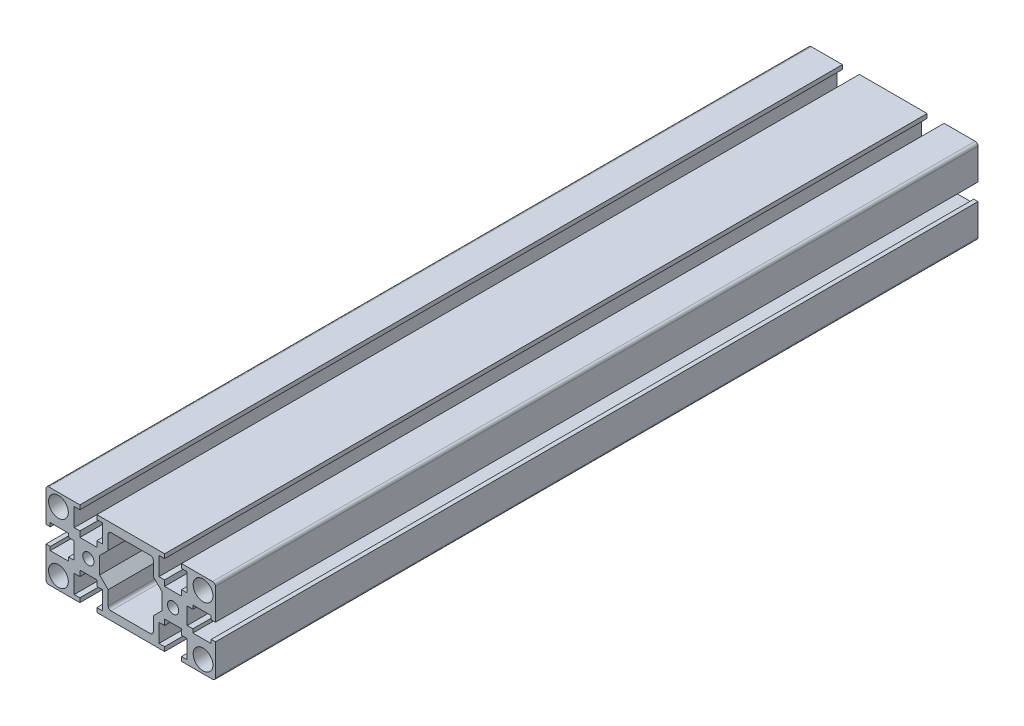
SolidWorks part; units mm, degrees
ref_plane "Front Plane" through (0, 0, 0) normal (0, 0, 1) x (1, 0, 0)
ref_plane "Top Plane" through (0, 0, 0) normal (0, 1, 0) x (1, 0, 0)
ref_plane "Right Plane" through (0, 0, 0) normal (1, 0, 0) x (0, 0, -1)
sketch "Sketch1" plane through (0, 0, 0) normal (0, 0, 1) x (1, 0, 0)
  line L0 (-49.2543, 0) -> (49.2543, 0) construction
  line L1 (-15, -15) -> (15, -15) construction
  line L2 (-15, -15) -> (-15, 14) construction
  line L3 (-14, 15) -> (15, 15) construction
  line L4 (15, -15) -> (15, 15) construction
  line L5 (-15, -15) -> (15, 15) construction
  line L6 (-15, 15) -> (15, -15) construction
  line L7 (-5, -3) -> (-5, 3)
  line L8 (-5, 3) -> (-7, 3)
  line L9 (-7, 3) -> (-7, 4.2984)
  line L10 (-7, 4.2984) -> (-13.5, 4.2984)
  line L11 (-13.5, 4.2984) -> (-13.5, 3)
  line L12 (-13.5, 3) -> (-15, 3)
  line L13 (-15, 3) -> (-15, 14)
  line L14 (-14, 15) -> (-3, 15)
  line L15 (-3, 15) -> (-3, 13.5)
  line L16 (-3, 13.5) -> (-5, 13.5)
  line L17 (-5, 13.5) -> (-5, 7)
  line L18 (-5, 7) -> (-3, 7)
  line L19 (-3, 7) -> (-3, 5)
  line L20 (-3, 5) -> (3, 5)
  line L21 (3, 15) -> (3, 13.5)
  line L22 (3, 13.5) -> (5, 13.5)
  line L23 (5, 13.5) -> (5, 7)
  line L24 (5, 7) -> (3, 7)
  line L25 (3, 7) -> (3, 5)
  line L26 (0, -31.6943) -> (0, 31.6943) construction
  line L27 (3, 15) -> (27, 15)
  line L28 (4, -3) -> (4, 3)
  line L29 (4, 3) -> (7, 6)
  line L30 (7, 6) -> (7, 11)
  line L31 (8, 12) -> (22, 12)
  line L32 (5, -7) -> (3, -7)
  line L33 (4, -3) -> (7, -6)
  line L34 (7, -6) -> (7, -11)
  line L35 (8, -12) -> (22, -12)
  line L36 (3, -15) -> (27, -15)
  line L37 (3, -15) -> (3, -13.5)
  line L38 (3, -13.5) -> (5, -13.5)
  line L39 (5, -13.5) -> (5, -7)
  line L40 (3, -7) -> (3, -5)
  line L41 (-3, -5) -> (3, -5)
  line L42 (-3, -7) -> (-3, -5)
  line L43 (-5, -7) -> (-3, -7)
  line L44 (-5, -13.5) -> (-5, -7)
  line L45 (-3, -13.5) -> (-5, -13.5)
  line L46 (-3, -15) -> (-3, -13.5)
  line L47 (-14, -15) -> (-3, -15)
  line L48 (-13.5, -3) -> (-15, -3)
  line L49 (-15, -3) -> (-15, -14)
  line L50 (-13.5, -4.2984) -> (-13.5, -3)
  line L51 (-7, -4.2984) -> (-13.5, -4.2984)
  line L52 (-7, -3) -> (-7, -4.2984)
  line L53 (-5, -3) -> (-7, -3)
  line L54 (26, 3) -> (23, 6)
  line L55 (23, 6) -> (23, 11)
  line L56 (27, 15) -> (27, 13.5)
  line L57 (27, 13.5) -> (25, 13.5)
  line L58 (25, 13.5) -> (25, 7)
  line L59 (25, 7) -> (27, 7)
  line L60 (27, 7) -> (27, 5)
  line L61 (33, 7) -> (33, 5)
  line L62 (33, 5) -> (27, 5)
  line L63 (35, 7) -> (33, 7)
  line L64 (35, 13.5) -> (35, 7)
  line L65 (33, 15) -> (33, 13.5)
  line L66 (33, 13.5) -> (35, 13.5)
  line L67 (44, 15) -> (33, 15)
  line L68 (45, 3) -> (45, 14)
  line L69 (43.5, 3) -> (45, 3)
  line L70 (43.5, 4.2984) -> (43.5, 3)
  line L71 (37, 4.2984) -> (43.5, 4.2984)
  line L72 (37, 3) -> (37, 4.2984)
  line L73 (35, 3) -> (37, 3)
  line L74 (35, -3) -> (35, 3)
  line L75 (35, -3) -> (37, -3)
  line L76 (37, -3) -> (37, -4.2984)
  line L77 (43.5, -3) -> (45, -3)
  line L78 (43.5, -4.2984) -> (43.5, -3)
  line L79 (37, -4.2984) -> (43.5, -4.2984)
  line L80 (45, -3) -> (45, -14)
  line L81 (44, -15) -> (33, -15)
  line L82 (33, -15) -> (33, -13.5)
  line L83 (35, -13.5) -> (35, -7)
  line L84 (35, -7) -> (33, -7)
  line L85 (33, -7) -> (33, -5)
  line L86 (33, -5) -> (27, -5)
  line L87 (27, -7) -> (27, -5)
  line L88 (25, -7) -> (27, -7)
  line L89 (26, -3) -> (26, 3)
  line L90 (26, -3) -> (23, -6)
  line L91 (23, -6) -> (23, -11)
  line L92 (25, -13.5) -> (25, -7)
  line L93 (27, -13.5) -> (25, -13.5)
  line L94 (27, -15) -> (27, -13.5)
  line L95 (33, -13.5) -> (35, -13.5)
  circle A0 centre (0, 0) radius 2
  circle A1 centre (-10.6066, 10.6066) radius 3.5
  arc A2 (-15, 14) -> (-14, 15) centre (-14, 14) cw
  arc A3 (7, 11) -> (8, 12) centre (8, 11) cw
  arc A4 (7, -11) -> (8, -12) centre (8, -11) ccw
  arc A5 (-15, -14) -> (-14, -15) centre (-14, -14) ccw
  arc A6 (23, 11) -> (22, 12) centre (22, 11) ccw
  circle A7 centre (40.6066, 10.6066) radius 3.5
  arc A8 (45, 14) -> (44, 15) centre (44, 14) ccw
  circle A9 centre (30, 0) radius 2
  arc A10 (45, -14) -> (44, -15) centre (44, -14) cw
  arc A11 (23, -11) -> (22, -12) centre (22, -11) cw
  circle A12 centre (40.6066, -10.6066) radius 3.5
  circle A13 centre (-10.6066, -10.6066) radius 3.5
  point P0 (0, 0)
  point P9 (0, 0)
  point P35 (0, 0)
  point P39 (0, 5)
  point P49 (4, 0)
  point P73 (-5, 0)
  point P78 (15, 12)
  point P126 (15, -12)
  dimension "D3" = 4
  dimension "D4" = 7
  dimension "D11" = 1
  dimension "D21" = 1
  dimension "D1" = 30
  dimension "D2" = 30
  dimension "D5" = 15
  dimension "D6" = 12
  dimension "D7" = 3
  dimension "D8" = 2
  dimension "D9" = 6.5
  dimension "D10" = 1.5
  dimension "D12" = 1.5
  dimension "D13" = 5
  dimension "D14" = 2
  dimension "D15" = 4
  dimension "D16" = 2
  dimension "D17" = 2
  dimension "D18" = 3
  dimension "D19" = 3
extrude "Boss-Extrude1" add sketch "Sketch1" along normal blind 270
